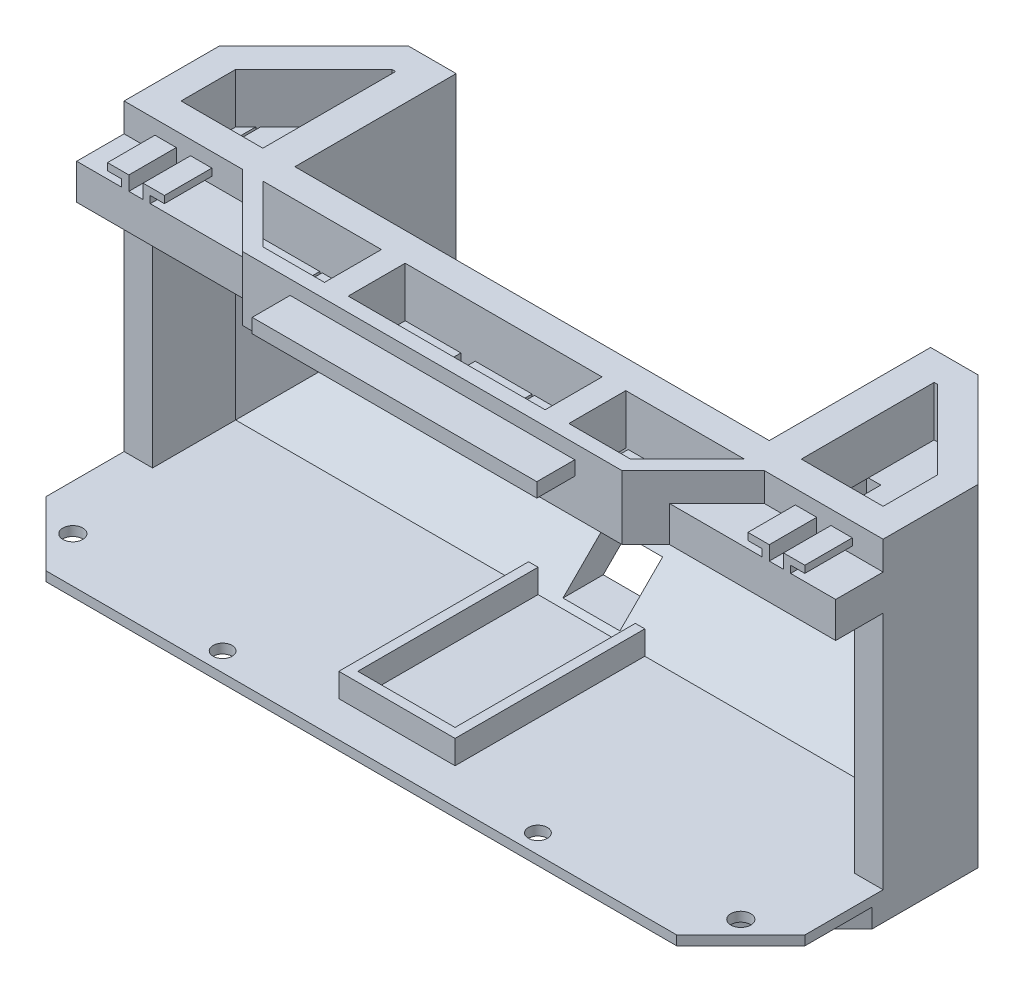
SolidWorks part; units mm, degrees
ref_plane "Front Plane" through (0, 0, 0) normal (0, 0, 1) x (1, 0, 0)
ref_plane "Top Plane" through (0, 0, 0) normal (0, 1, 0) x (1, 0, 0)
ref_plane "Right Plane" through (0, 0, 0) normal (1, 0, 0) x (0, 0, -1)
sketch "Sketch2" plane through (0, 0, 0) normal (0, 1, 0) x (1, 0, 0)
  line L0 (-62.5376, 36.5919) -> (57.4624, 36.5919)
  line L1 (57.4624, 36.5919) -> (77.4624, 16.5919)
  line L2 (77.4624, 16.5919) -> (77.4624, -3.4081)
  line L3 (77.4624, -3.4081) -> (52.4624, -3.4081)
  line L4 (52.4624, -3.4081) -> (37.4624, -18.4081)
  line L5 (37.4624, -18.4081) -> (-42.5376, -18.4081)
  line L6 (-42.5376, -18.4081) -> (-57.5376, -3.4081)
  line L7 (-57.5376, -3.4081) -> (-82.5376, -3.4081)
  line L8 (-82.5376, -3.4081) -> (-82.5376, 16.5919)
  line L9 (-82.5376, 16.5919) -> (-62.5376, 36.5919)
  dimension "D1" = 135
  dimension "D2" = 135
  dimension "D3" = 135
  dimension "D4" = 20
  dimension "D5" = 20
  dimension "D6" = 20
  dimension "D7" = 25
  dimension "D8" = 25
  dimension "D9" = 80
  dimension "D10" = 160
  dimension "D11" = 15
extrude "Boss-Extrude1" add sketch "Sketch2" along normal blind 70
sketch "Sketch3" plane through (0, 0, 0) normal (1, 0, 0) x (0, 0, -1)
  line L0 (16.5919, 0) -> (36.5919, 20)
  line L1 (36.5919, 70) -> (36.5919, 0) construction
  line L2 (36.5919, 20) -> (36.5919, 0)
  line L3 (36.5919, 0) -> (16.5919, 0)
  line L4 (36.5919, 70) -> (16.5919, 70) construction
  dimension "D1" = 50
extrude "Cut-Extrude1" cut sketch "Sketch3" against normal through all both and the other way through all
shell "Shell1" thickness 6
sketch "Sketch5" plane through (0, 0, 0) normal (0, -1, 0) x (1, 0, 0)
  line L0 (-82.5376, -16.5919) -> (-82.5376, 3.4081) construction
  line L1 (77.4624, -16.5919) -> (-82.5376, -16.5919)
  line L2 (77.4624, -16.5919) -> (77.4624, 5.7304)
  line L3 (59.7848, 23.4081) -> (-64.8599, 23.4081)
  line L4 (-82.5376, -16.5919) -> (-82.5376, 5.7304)
  line L5 (-82.5376, 5.7304) -> (-64.8599, 23.4081)
  line L6 (77.4624, 5.7304) -> (59.7848, 23.4081)
  dimension "D1" = 40
  dimension "D2" = 25
  dimension "D3" = 135
  dimension "D4" = 135
  dimension "D5" = 25
extrude "Boss-Extrude2" add sketch "Sketch5" against normal blind 6
sketch "Sketch6" plane through (0, 6, 0) normal (0, 1, 0) x (1, 0, 0)
  line L6 (-82.5376, -5.7304) -> (-82.5376, -19.8726)
  line L7 (77.4624, -5.7304) -> (77.4624, -19.8726)
  line L8 (-82.5376, -5.7304) -> (77.4624, -5.7304)
  line L9 (84.5335, -12.8015) -> (63.9269, -33.4081)
  line L10 (63.9269, -33.4081) -> (-69.002, -33.4081)
  line L11 (-69.002, -33.4081) -> (-89.6086, -12.8015)
  line L12 (77.4624, -19.8726) -> (63.9269, -33.4081)
  line L13 (63.9269, -33.4081) -> (-69.002, -33.4081)
  line L14 (-69.002, -33.4081) -> (-82.5376, -19.8726)
  dimension "D1" = 10
extrude "Boss-Extrude3" add sketch "Sketch6" against normal blind 2
sketch "Sketch7" plane through (0, 4, 0) normal (0, -1, 0) x (1, 0, 0)
  line L0 (70.6947, 26.6403) -> (67.8663, 23.8119) construction
  line L1 (63.9269, 33.4081) -> (77.4624, 19.8726) construction
  line L2 (-2.5376, 33.4081) -> (63.9269, 33.4081) construction
  line L3 (-69.002, 33.4081) -> (63.9269, 33.4081) construction
  line L4 (30.6947, 33.4081) -> (30.6947, 29.4081) construction
  line L5 (-2.5376, 33.4081) -> (-2.5376, 26.6403) construction
  circle A0 centre (67.8663, 23.8119) radius 2.1
  circle A2 centre (30.6947, 29.4081) radius 2
  circle A3 centre (-72.9414, 23.8119) radius 2.1
  circle A4 centre (-35.7698, 29.4081) radius 2
  dimension "D2" = 4.2
  dimension "D4" = 4
  dimension "D1" = 4
  dimension "D3" = 90
  dimension "D5" = 4
extrude "Cut-Extrude5" cut sketch "Sketch7" against normal up to next
sketch "Sketch8" plane through (0, 0, 3.4081) normal (0, 0, 1) x (1, 0, 0)
  line L0 (-70.0376, 70) -> (-70.0376, 64) construction
  line L1 (-82.5376, 70) -> (-57.5376, 70) construction
  line L2 (-60.0523, 64) -> (-76.5376, 64) construction
  line L3 (-42.5376, 70) -> (37.4624, 70) construction
  line L4 (-2.5376, 70) -> (-2.5376, 64) construction
  line L5 (54.9772, 64) -> (-60.0523, 64) construction
  line L6 (-73.0376, 64) -> (-73.0376, 65.5)
  line L7 (-76.5376, 64) -> (-57.5376, 64) construction
  line L8 (-73.0376, 65.5) -> (-76.0376, 65.5)
  line L9 (-76.0376, 65.5) -> (-76.0376, 67)
  line L10 (-76.0376, 67) -> (-71.5376, 67)
  line L11 (-71.5376, 67) -> (-71.5376, 64)
  line L12 (-71.5376, 64) -> (-73.0376, 64)
  line L13 (-68.5376, 67) -> (-68.5376, 64)
  line L14 (-64.0376, 67) -> (-68.5376, 67)
  line L15 (-64.0376, 65.5) -> (-64.0376, 67)
  line L16 (-67.0376, 65.5) -> (-64.0376, 65.5)
  line L17 (-67.0376, 64) -> (-67.0376, 65.5)
  line L18 (-68.5376, 64) -> (-67.0376, 64)
  line L19 (58.9624, 67) -> (63.4624, 67)
  line L20 (58.9624, 65.5) -> (58.9624, 67)
  line L21 (61.9624, 65.5) -> (58.9624, 65.5)
  line L22 (61.9624, 64) -> (61.9624, 65.5)
  line L23 (63.4624, 64) -> (61.9624, 64)
  line L24 (63.4624, 67) -> (63.4624, 64)
  line L25 (66.4624, 67) -> (66.4624, 64)
  line L26 (70.9624, 67) -> (66.4624, 67)
  line L27 (70.9624, 65.5) -> (70.9624, 67)
  line L28 (67.9624, 65.5) -> (70.9624, 65.5)
  line L29 (67.9624, 64) -> (67.9624, 65.5)
  line L30 (66.4624, 64) -> (67.9624, 64)
  point P16 (-76.0376, 66.25)
  point P21 (-72.2876, 64)
  dimension "D1" = 1.5
  dimension "D2" = 1.5
  dimension "D3" = 4.5
  dimension "D4" = 1.5
  dimension "D5" = 3
extrude "Boss-Extrude4" add sketch "Sketch8" along normal blind 10
sketch "Sketch9" plane through (0, 70, 0) normal (0, 1, 0) x (1, 0, 0)
  line L0 (-76.5376, 14.1066) -> (-60.0523, 30.5919)
  line L1 (-60.0523, 30.5919) -> (-59.2949, 30.5919)
  line L2 (-59.2949, 30.5919) -> (-59.2949, 2.5919)
  line L3 (-59.2949, 2.5919) -> (-76.5376, 2.5919)
  line L4 (-76.5376, 2.5919) -> (-76.5376, 14.1066)
  line L5 (-53.2949, -3.4081) -> (-41.2949, -15.4081)
  line L6 (-41.2949, -15.4081) -> (-28.2949, -15.4081)
  line L7 (-28.2949, -15.4081) -> (-28.2949, -3.4081)
  line L8 (-28.2949, -3.4081) -> (-53.2949, -3.4081)
  line L9 (-23.2949, -3.4081) -> (-23.2949, -15.4081)
  line L13 (-2.5376, -18.4081) -> (-2.5376, 12.4152) construction
  line L14 (-42.5376, -18.4081) -> (37.4624, -18.4081) construction
  line L15 (-23.2949, -3.4081) -> (18.2198, -3.4081)
  line L16 (-23.2949, -15.4081) -> (18.2198, -15.4081)
  line L17 (-53.2949, -3.4081) -> (-60.2217, 3.5186) construction
  line L18 (-57.5376, -3.4081) -> (-42.5376, -18.4081) construction
  line L19 (-82.5376, -3.4081) -> (-57.5376, -3.4081) construction
  line L20 (-62.5376, 36.5919) -> (-82.5376, 16.5919) construction
  line L21 (-82.5376, 16.5919) -> (-82.5376, -3.4081) construction
  line L22 (57.4624, 36.5919) -> (-62.5376, 36.5919) construction
  line L23 (18.2198, -3.4081) -> (18.2198, -15.4081)
  line L24 (23.2198, -15.4081) -> (23.2198, -3.4081)
  line L25 (36.2198, -15.4081) -> (23.2198, -15.4081)
  line L26 (48.2198, -3.4081) -> (36.2198, -15.4081)
  line L27 (23.2198, -3.4081) -> (48.2198, -3.4081)
  line L28 (54.2198, 2.5919) -> (71.4624, 2.5919)
  line L29 (54.2198, 30.5919) -> (54.2198, 2.5919)
  line L30 (54.9772, 30.5919) -> (54.2198, 30.5919)
  line L31 (71.4624, 14.1066) -> (54.9772, 30.5919)
  line L32 (71.4624, 2.5919) -> (71.4624, 14.1066)
  point P25 (-76.5376, 8.3492)
  point P31 (-2.5376, -15.4081)
  point P32 (-2.5376, -3.4081)
  dimension "D1" = 135
  dimension "D2" = 3
  dimension "D3" = 3
  dimension "D4" = 6
  dimension "D5" = 6
  dimension "D6" = 6
  dimension "D7" = 6
  dimension "D8" = 12
  dimension "D9" = 5
  dimension "D10" = 25
extrude "Cut-Extrude6" cut sketch "Sketch9" against normal up to next
sketch "Sketch10" plane through (0, 0, 0) normal (0, 0, 1) x (1, 0, 0)
  line L1 (-82.5376, 0) -> (77.4624, 0) construction
  line L2 (-8.5376, 7) -> (-8.5376, 16)
  line L3 (-8.5376, 16) -> (3.4624, 16)
  line L4 (3.4624, 16) -> (3.4624, 7)
  line L7 (-2.5376, 0) -> (-2.5376, 7) construction
  line L8 (-2.5376, 7) -> (-8.5376, 7)
  line L9 (-2.5376, 7) -> (3.4624, 7)
  dimension "D1" = 12
  dimension "D2" = 7
  dimension "D3" = 9
extrude "Cut-Extrude7" cut sketch "Sketch10" against normal through all
sketch "Sketch11" plane through (0, 0, 18.4081) normal (0, 0, 1) x (1, 0, 0)
  line L0 (54.2198, 64) -> (-59.2949, 64) construction
  line L1 (-32.5376, 64) -> (27.4624, 64)
  line L2 (-32.5376, 64) -> (-32.5376, 67)
  line L3 (-32.5376, 67) -> (27.4624, 67)
  line L4 (27.4624, 64) -> (27.4624, 67)
  line L5 (-42.5376, 70) -> (37.4624, 70) construction
  point P6 (-2.5376, 67)
  point P9 (-2.5376, 70)
  dimension "D1" = 3
  dimension "D2" = 60
extrude "Boss-Extrude5" add sketch "Sketch11" along normal blind 8
sketch "Sketch12" plane through (0, 70, 0) normal (0, 1, 0) x (1, 0, 0)
  line L0 (57.4624, 36.5919) -> (-62.5376, 36.5919) construction
  line L1 (-52.5376, 2.5919) -> (47.4624, 2.5919)
  line L2 (-52.5376, 2.5919) -> (-52.5376, 36.5919)
  line L3 (-52.5376, 36.5919) -> (47.4624, 36.5919)
  line L4 (47.4624, 2.5919) -> (47.4624, 36.5919)
  line L7 (18.2198, -3.4081) -> (-23.2949, -3.4081) construction
  line L8 (27.4624, -26.4081) -> (-32.5376, -26.4081) construction
  point P6 (-2.5376, 36.5919)
  point P9 (-2.5376, -26.4081)
  dimension "D1" = 100
  dimension "D3" = 6
extrude "Cut-Extrude8" cut sketch "Sketch12" against normal blind 50
sketch "Sketch13" plane through (0, 20, 0) normal (0, 1, 0) x (1, 0, 0)
  line L0 (47.4624, 28.1066) -> (47.4624, 36.5919) construction
  line L1 (-52.5376, 28.1066) -> (43.9772, 28.1066)
  line L3 (-49.0523, 30.5919) -> (47.4624, 30.5919)
  line L5 (47.4624, 30.5919) -> (54.9772, 30.5919) construction
  line L6 (-59.2949, 2.5919) -> (-59.2949, 30.5919) construction
  line L7 (-49.0523, 30.5919) -> (-56.2949, 30.5919)
  line L9 (-52.5376, 28.1066) -> (-56.2949, 28.1066)
  line L10 (-56.2949, 30.5919) -> (-56.2949, 28.1066)
  line L11 (47.4624, 30.5919) -> (51.2198, 30.5919)
  line L13 (43.9772, 28.1066) -> (51.2198, 28.1066)
  line L14 (51.2198, 30.5919) -> (51.2198, 28.1066)
  line L15 (54.2198, 30.5919) -> (54.2198, 2.5919) construction
  dimension "D1" = 3
  dimension "D2" = 3
extrude "Boss-Extrude8" add sketch "Sketch13" along normal blind 7
sketch "Sketch14" plane through (0, 20, 0) normal (0, 1, 0) x (1, 0, 0)
  line L0 (47.4624, 30.5919) -> (47.4624, 36.5919) construction
  line L1 (-52.5376, 36.5919) -> (47.4624, 36.5919)
  line L2 (-52.5376, 36.5919) -> (-52.5376, 33.5919)
  line L3 (-52.5376, 33.5919) -> (47.4624, 33.5919)
  line L4 (47.4624, 36.5919) -> (47.4624, 33.5919)
extrude "Boss-Extrude9" add sketch "Sketch14" along normal blind 10
sketch "Sketch15" plane through (0, 0, -2.5919) normal (0, 0, -1) x (-1, 0, 0)
  line L0 (52.5376, 30) -> (52.5376, 70) construction
  line L1 (-47.4624, 64) -> (52.5376, 64)
  line L2 (-47.4624, 64) -> (-47.4624, 66)
  line L3 (-47.4624, 66) -> (52.5376, 66)
  line L4 (52.5376, 64) -> (52.5376, 66)
  dimension "D1" = 2
extrude "Boss-Extrude10" add sketch "Sketch15" along normal blind 3
sketch "Sketch16" plane through (0, 6, 0) normal (0, 1, 0) x (1, 0, 0)
  line L0 (-76.5376, 14.1066) -> (71.4624, 14.1066) construction
  line L1 (-12.7876, -23.8934) -> (7.7124, -23.8934)
  line L2 (-12.7876, -23.8934) -> (-12.7876, -25.8934)
  line L3 (-12.7876, -25.8934) -> (7.7124, -25.8934)
  line L4 (7.7124, -23.8934) -> (7.7124, -25.8934)
  line L6 (7.7124, -25.8934) -> (9.7124, -25.8934)
  line L7 (7.7124, -25.8934) -> (7.7124, 14.1066)
  line L8 (7.7124, 14.1066) -> (9.7124, 14.1066)
  line L9 (9.7124, -25.8934) -> (9.7124, 14.1066)
  line L10 (-12.7876, -25.8934) -> (-14.7876, -25.8934)
  line L11 (-12.7876, -25.8934) -> (-12.7876, 14.1066)
  line L12 (-12.7876, 14.1066) -> (-14.7876, 14.1066)
  line L13 (-14.7876, -25.8934) -> (-14.7876, 14.1066)
  point P12 (-2.5376, -23.8934)
  point P13 (-2.5376, 14.1066)
  line M22 (71.4624, 14.1066) -> (-76.5376, 14.1066)
  dimension "D1" = 38
  dimension "D2" = 2
  dimension "D3" = 20.5
  dimension "D4" = 2
  dimension "D5" = 2
extrude "Boss-Extrude11" add sketch "Sketch16" along normal blind 5 contours L13 L10 L2 L11 M22 | L4 L1 L2 L3 | L6 L9 L7 L4 M22
ref_plane "Plane1" through (0, 59.5, 0) normal (0, 1, 0) x (1, 0, 0)
sketch "Sketch17" plane through (0, 59.5, 0) normal (0, 1, 0) x (1, 0, 0)
  line L0 (-76.5376, 14.1066) -> (-60.0523, 30.5919)
  line L1 (-60.0523, 30.5919) -> (-56.2949, 30.5919)
  line L2 (-60.0523, 30.5919) -> (-56.2949, 30.5919) construction
  line L3 (-56.2949, 30.5919) -> (-56.2949, -0.4081)
  line L6 (-59.2949, 2.5919) -> (-59.2949, 30.5919) construction
  line L8 (-76.5376, 14.1066) -> (-76.5376, -0.4081)
  line L22 (51.2198, 30.5919) -> (54.9772, 30.5919)
  line L23 (-25.2949, -18.4081) -> (-25.2949, -0.4081)
  line L24 (-42.5376, -18.4081) -> (-25.2949, -18.4081)
  line L25 (-60.5376, -0.4081) -> (-42.5376, -18.4081)
  line L26 (-25.2949, -0.4081) -> (-60.5376, -0.4081)
  line L28 (-42.5376, -18.4081) -> (-25.2949, -18.4081)
  line L29 (-60.5376, -0.4081) -> (-42.5376, -18.4081)
  line L30 (-25.2949, -0.4081) -> (-56.2949, -0.4081)
  line L31 (21.2198, -0.4081) -> (21.2198, -18.4081)
  line L32 (21.2198, -18.4081) -> (37.4624, -18.4081)
  line L33 (37.4624, -18.4081) -> (55.4624, -0.4081)
  line L34 (55.4624, -0.4081) -> (21.2198, -0.4081)
  line L36 (21.2198, -18.4081) -> (37.4624, -18.4081)
  line L38 (37.4624, -18.4081) -> (55.4624, -0.4081)
  line L39 (51.2198, -0.4081) -> (21.2198, -0.4081)
  line L40 (54.9772, 30.5919) -> (71.4624, 14.1066)
  line L41 (21.2198, -18.4081) -> (21.2198, -0.4081)
  line L42 (21.2198, -0.4081) -> (-25.2949, -0.4081)
  line L43 (-25.2949, -0.4081) -> (-25.2949, -18.4081)
  line L44 (-25.2949, -18.4081) -> (21.2198, -18.4081)
  line L45 (-76.5376, 2.5919) -> (-59.2949, 2.5919) construction
  line L46 (21.2198, -0.4081) -> (-25.2949, -0.4081)
  line L48 (-25.2949, -18.4081) -> (21.2198, -18.4081)
  line L49 (51.2198, -0.4081) -> (71.4624, -0.4081)
  line L50 (51.2198, 30.5919) -> (51.2198, -0.4081)
  line L51 (55.4624, -0.4081) -> (71.4624, -0.4081)
  line L52 (51.2198, 30.5919) -> (51.2198, -0.4081)
  line L53 (71.4624, 14.1066) -> (71.4624, -0.4081)
  line L54 (-76.5376, -0.4081) -> (-60.5376, -0.4081)
  dimension "D1" = 3
  dimension "D2" = 3
  dimension "D3" = 3
  dimension "D4" = 3
  dimension "D5" = 3
  dimension "D6" = 3
extrude "Boss-Extrude12" add sketch "Sketch17" against normal blind 3
sketch "Sketch18" plane through (0, 59.5, 0) normal (0, 1, 0) x (1, 0, 0)
  line L0 (-56.2949, 30.5919) -> (-59.2949, 30.5919)
  line L1 (-59.2949, 30.5919) -> (-59.2949, 2.5919)
  line L2 (-59.2949, 2.5919) -> (-76.5376, 2.5919)
  line L3 (-76.5376, 2.5919) -> (-76.5376, -0.4081)
  line L4 (-76.5376, -0.4081) -> (-60.5376, -0.4081)
  line L5 (-60.5376, -0.4081) -> (-42.5376, -18.4081)
  line L6 (-42.5376, -18.4081) -> (37.4624, -18.4081)
  line L7 (37.4624, -18.4081) -> (55.4624, -0.4081)
  line L8 (55.4624, -0.4081) -> (71.4624, -0.4081)
  line L9 (71.4624, -0.4081) -> (71.4624, 2.5919)
  line L10 (71.4624, 2.5919) -> (54.2198, 2.5919)
  line L11 (54.2198, 2.5919) -> (54.2198, 30.5919)
  line L12 (54.2198, 30.5919) -> (51.2198, 30.5919)
  line L13 (51.2198, 30.5919) -> (51.2198, -0.4081)
  line L14 (51.2198, -0.4081) -> (-56.2949, -0.4081)
  line L15 (-56.2949, -0.4081) -> (-56.2949, 30.5919)
  line L16 (-53.2949, -3.4081) -> (-41.2949, -15.4081)
  line L17 (-41.2949, -15.4081) -> (-28.2949, -15.4081)
  line L18 (-28.2949, -15.4081) -> (-28.2949, -3.4081)
  line L19 (-28.2949, -3.4081) -> (-53.2949, -3.4081)
  line L20 (18.2198, -3.4081) -> (-23.2949, -3.4081)
  line L21 (-23.2949, -3.4081) -> (-23.2949, -15.4081)
  line L22 (-23.2949, -15.4081) -> (18.2198, -15.4081)
  line L23 (18.2198, -15.4081) -> (18.2198, -3.4081)
  line L24 (23.2198, -3.4081) -> (23.2198, -15.4081)
  line L25 (23.2198, -15.4081) -> (36.2198, -15.4081)
  line L26 (36.2198, -15.4081) -> (48.2198, -3.4081)
  line L27 (48.2198, -3.4081) -> (23.2198, -3.4081)
extrude "Boss-Extrude13" add sketch "Sketch18" along normal up to surface (10.5 mm away) up to face at (-66.3434, 70, -16.0948)
sketch "Sketch19" plane through (0, 59.5, 0) normal (0, 1, 0) x (1, 0, 0)
  line L0 (-41.2949, -15.4081) -> (-28.2949, -15.4081) construction
  line L1 (-28.7949, -3.4081) -> (-40.7949, -3.4081) construction
  line L2 (-28.7949, -3.4081) -> (-28.7949, -15.4081) construction
  line L3 (-28.7949, -15.4081) -> (-40.7949, -15.4081) construction
  line L4 (-40.7949, -3.4081) -> (-40.7949, -15.4081) construction
  line L5 (-61.9162, 16.7279) -> (-73.9162, 16.7279) construction
  line L6 (-61.9162, 16.7279) -> (-61.9162, 4.7279) construction
  line L7 (-61.9162, 4.7279) -> (-73.9162, 4.7279) construction
  line L8 (-73.9162, 16.7279) -> (-73.9162, 4.7279) construction
  line L9 (3.4624, -3.4081) -> (-8.5376, -3.4081) construction
  line L10 (3.4624, -3.4081) -> (3.4624, -15.4081) construction
  line L11 (3.4624, -15.4081) -> (-8.5376, -15.4081) construction
  line L12 (-8.5376, -3.4081) -> (-8.5376, -15.4081) construction
  line L13 (35.7198, -3.4081) -> (23.7198, -3.4081) construction
  line L14 (35.7198, -3.4081) -> (35.7198, -15.4081) construction
  line L15 (35.7198, -15.4081) -> (23.7198, -15.4081) construction
  line L16 (23.7198, -3.4081) -> (23.7198, -15.4081) construction
  line L17 (68.8411, 16.7279) -> (56.8411, 16.7279) construction
  line L18 (68.8411, 16.7279) -> (68.8411, 4.7279) construction
  line L19 (68.8411, 4.7279) -> (56.8411, 4.7279) construction
  line L20 (56.8411, 16.7279) -> (56.8411, 4.7279) construction
  line L21 (-28.2949, -15.4081) -> (-28.2949, -3.4081) construction
  line L23 (36.2198, -15.4081) -> (35.7198, -15.4081)
  line L24 (-60.0523, 30.5919) -> (-76.5376, 14.1066) construction
  line L25 (71.4624, 14.1066) -> (54.9772, 30.5919) construction
  line L26 (35.7198, -15.4081) -> (35.7198, -3.4081)
  line L27 (35.7198, -3.4081) -> (36.2198, -3.4081)
  line L28 (35.7198, -3.9081) -> (36.2198, -3.9081)
  line L29 (-23.2949, -15.4081) -> (18.2198, -15.4081) construction
  line L30 (18.2198, -15.4081) -> (18.2198, -3.4081) construction
  line L31 (23.2198, -15.4081) -> (36.2198, -15.4081) construction
  line L32 (-76.5376, 2.5919) -> (-59.2949, 2.5919) construction
  line L33 (54.2198, 2.5919) -> (71.4624, 2.5919) construction
  line L34 (-61.4162, 16.7279) -> (-61.4162, 4.7279)
  line L35 (-74.4162, 16.2279) -> (-74.4162, 4.7279)
  line L36 (-73.9162, 16.7279) -> (-74.4162, 16.2279)
  line L37 (-60.0523, 30.5919) -> (-76.5376, 14.1066) construction
  line L38 (-74.4162, 4.7279) -> (-73.9162, 4.7279)
  line L39 (-74.4162, 16.7279) -> (-74.4162, 4.7279) construction
  line L40 (-73.9162, 4.7279) -> (-73.9162, 16.7279)
  line L41 (-61.4162, 16.7279) -> (-61.9162, 16.7279)
  line L42 (-61.9162, 16.7279) -> (-61.9162, 4.7279)
  line L43 (-61.9162, 4.7279) -> (-61.4162, 4.7279)
  line L44 (-41.2949, -3.4081) -> (-41.2949, -15.4081)
  line L45 (-28.7949, -3.4081) -> (-28.2949, -3.4081)
  line L46 (-28.2949, -3.4081) -> (-28.2949, -15.4081)
  line L47 (-28.2949, -15.4081) -> (-28.7949, -15.4081)
  line L48 (-28.7949, -15.4081) -> (-28.7949, -3.4081)
  line L49 (-41.2949, -15.4081) -> (-40.7949, -15.4081)
  line L50 (-40.7949, -15.4081) -> (-40.7949, -3.4081)
  line L51 (-40.7949, -3.4081) -> (-41.2949, -3.4081)
  line L52 (-9.0376, -3.4081) -> (-9.0376, -15.4081)
  line L53 (3.9624, -3.4081) -> (3.9624, -15.4081)
  line L54 (-9.0376, -3.4081) -> (-8.5376, -3.4081)
  line L55 (-8.5376, -3.4081) -> (-8.5376, -15.4081)
  line L56 (-8.5376, -15.4081) -> (-9.0376, -15.4081)
  line L57 (3.9624, -3.4081) -> (3.4624, -3.4081)
  line L58 (3.4624, -3.4081) -> (3.4624, -15.4081)
  line L59 (3.4624, -15.4081) -> (3.9624, -15.4081)
  line L60 (36.2198, -3.4081) -> (36.2198, -15.4081)
  line L61 (23.7198, -3.4081) -> (23.2198, -3.4081)
  line L62 (23.2198, -3.4081) -> (23.2198, -15.4081)
  line L63 (23.2198, -15.4081) -> (23.7198, -15.4081)
  line L64 (23.7198, -15.4081) -> (23.7198, -3.4081)
  line L66 (56.3411, 16.7279) -> (56.3411, 4.7279)
  line L71 (56.3411, 4.7279) -> (56.8411, 4.7279)
  line L72 (56.8411, 4.7279) -> (56.8411, 16.7279)
  line L73 (56.8411, 16.7279) -> (56.3411, 16.7279)
  line L75 (69.3411, 16.2279) -> (69.3411, 4.7279)
  line L76 (68.8411, 16.7279) -> (69.3411, 16.2279)
  line L77 (71.4624, 14.1066) -> (54.9772, 30.5919) construction
  line L78 (69.3411, 4.7279) -> (68.8411, 4.7279)
  line L79 (68.8411, 4.7279) -> (68.8411, 16.7279)
  line L81 (69.3411, 16.7279) -> (69.3411, 4.7279) construction
  point P20 (-34.7949, -15.4081)
  point P23 (-34.7949, -15.4081)
  point P26 (-28.2949, -9.4081)
  point P27 (-28.7949, -9.4081)
  point P28 (-67.9162, 4.7279)
  point P31 (-67.9162, 2.5919)
  point P32 (62.8411, 4.7279)
  point P35 (62.8411, 2.5919)
  point P47 (-2.5376, -15.4081)
  point P50 (-2.5376, -15.4081)
  point P51 (3.4624, -9.4081)
  point P54 (18.2198, -9.4081)
  point P55 (29.7198, -15.4081)
  point P58 (29.7198, -15.4081)
  point P77 (69.3411, 16.7279)
  point P78 (69.3411, 4.7279)
  dimension "D1" = 12
  dimension "D2" = 12
  dimension "D3" = 0.5
  dimension "D4" = 0.5
  dimension "D5" = 0.5
  dimension "D6" = 0.5
  dimension "D7" = 0.5
  dimension "D8" = 0.5
  dimension "D9" = 0.5
  dimension "D10" = 0.5
extrude "Cut-Extrude10" cut sketch "Sketch19" against normal up to surface (3 mm away) contours L34 L43 L42 L41 | L35 L38 L40 L36 | L50 L51 L44 L49 | L46 L47 L48 L45 | L55 L56 L52 L54 | L53 L59 L58 L57 | L64 L61 L62 L63 | L60 L23 L26 L27 | L66 L71 L72 L73 | L79 L76 L75 L78 up to face at (-2.5376, 56.5, -7.9511)
sketch "Sketch21" plane through (0, 56.5, 0) normal (0, -1, 0) x (-1, 0, 0)
  line L0 (61.4162, 4.7279) -> (61.9162, 4.7279) construction
  line L1 (28.7949, -15.4081) -> (25.7949, -15.4081)
  line L2 (28.7949, -15.4081) -> (28.7949, -3.4081)
  line L3 (28.7949, -3.4081) -> (25.7949, -3.4081)
  line L4 (25.7949, -15.4081) -> (25.7949, -3.4081)
  line L5 (61.9162, 16.7279) -> (58.9162, 16.7279)
  line L6 (61.9162, 16.7279) -> (61.9162, 4.7279)
  line L7 (61.9162, 4.7279) -> (58.9162, 4.7279)
  line L8 (58.9162, 16.7279) -> (58.9162, 4.7279)
  line L9 (8.5376, -3.4081) -> (9.0376, -3.4081) construction
  line L10 (8.5376, -15.4081) -> (11.5376, -15.4081)
  line L11 (8.5376, -15.4081) -> (8.5376, -3.4081)
  line L12 (8.5376, -3.4081) -> (11.5376, -3.4081)
  line L13 (11.5376, -15.4081) -> (11.5376, -3.4081)
  line L14 (-56.3411, 16.7279) -> (-56.8411, 16.7279) construction
  line L15 (-23.7198, -15.4081) -> (-20.7198, -15.4081)
  line L16 (-23.7198, -15.4081) -> (-23.7198, -3.4081)
  line L17 (-23.7198, -3.4081) -> (-20.7198, -3.4081)
  line L18 (-20.7198, -15.4081) -> (-20.7198, -3.4081)
  line L19 (-56.8411, 4.7279) -> (-53.8411, 4.7279)
  line L20 (-56.8411, 4.7279) -> (-56.8411, 16.7279)
  line L21 (-56.8411, 16.7279) -> (-53.8411, 16.7279)
  line L22 (-53.8411, 4.7279) -> (-53.8411, 16.7279)
  line L23 (-23.2198, -3.4081) -> (-23.7198, -3.4081) construction
  dimension "D1" = 3
  dimension "D2" = 3
  dimension "D3" = 3
  dimension "D4" = 3
  dimension "D5" = 3
extrude "Cut-Extrude11" cut sketch "Sketch21" against normal up to surface (3 mm away) up to face at (-69.8202, 59.5, -13.654)
sketch "Sketch22" plane through (0, 0, 0) normal (1, 0, 0) x (0, 0, -1)
  line L0 (5.5919, 66) -> (30.5919, 30)
  line L1 (30.5919, 56.5) -> (30.5919, 22.4853) construction
  line L2 (30.5919, 30) -> (30.5919, 27)
  line L3 (30.5919, 27) -> (28.1066, 27)
  line L4 (3.1278, 64.2888) -> (28.1278, 28.2888)
  line L5 (28.1066, 27) -> (28.1278, 28.2888)
  line L6 (3.1278, 64.2888) -> (5.5919, 66)
  dimension "D1" = 3
sketch "Sketch23" plane through (0, 27, 0) normal (0, 1, 0) x (1, 0, 0)
  line L0 (-52.5376, 36.5919) -> (-52.5376, 2.5919) construction
  line L1 (-56.2949, 30.5919) -> (-52.5376, 30.5919)
  line L2 (-56.2949, 30.5919) -> (-56.2949, 2.5919)
  line L3 (-56.2949, 2.5919) -> (-52.5376, 2.5919)
  line L4 (-52.5376, 30.5919) -> (-52.5376, 2.5919)
  line L5 (51.2198, 30.5919) -> (47.4624, 30.5919)
  line L6 (51.2198, 30.5919) -> (51.2198, 2.5919)
  line L7 (51.2198, 2.5919) -> (47.4624, 2.5919)
  line L8 (47.4624, 30.5919) -> (47.4624, 2.5919)
  line L9 (-52.5376, 2.5919) -> (47.4624, 2.5919) construction
  line L10 (47.4624, 2.5919) -> (47.4624, 36.5919) construction
extrude "Boss-Extrude15" add sketch "Sketch23" along normal up to surface (37 mm away)
extrude "Boss-Extrude16" add sketch "Sketch22" along normal up to surface (100 mm away) from surface at -52.5376 up to face at (47.4624, 44.6923, -19.3238) starting at face at (-52.5376, 44.6923, -19.3238)
sketch "Sketch24" plane through (0, 3.8155, -48.7755) normal (0, 0.5704, -0.8214) x (-1, 0, 0)
  line L0 (52.5376, 77.4194) -> (-47.4624, 77.4194) construction
  line L2 (52.5376, 75.7082) -> (-47.4624, 75.7082) construction
  circle A0 centre (2.5376, 57.7082) radius 5
  point P5 (2.5376, 77.4194)
  dimension "D2" = 10
  dimension "D1" = 18
extrude "Cut-Extrude12" cut sketch "Sketch24" against normal up to surface (3 mm away) up to face at (-2.5376, 46.1444, -15.7281)
sketch "Sketch26" plane through (0, 0, 0) normal (1, 0, 0) x (0, 0, -1)
  line L0 (28.1066, 27) -> (28.1278, 28.2888)
  line L1 (28.1278, 28.2888) -> (3.3283, 64)
  line L2 (3.3283, 64) -> (2.5919, 64)
  line L3 (2.5919, 64) -> (2.5919, 27)
  line L4 (2.5919, 27) -> (28.1066, 27)
extrude "Cut-Extrude13" cut sketch "Sketch26" along normal up to surface (107.5147 mm away) from surface at -56.2949 up to face at (51.2198, 34.9142, -20.4301) starting at face at (-56.2949, 34.9142, -20.4301)
sketch "Sketch27" plane through (0, 64, 0) normal (0, -1, 0) x (1, 0, 0)
  line L0 (-60.5376, 0.4081) -> (-42.5376, 18.4081) construction
  line L1 (-82.5376, 0.4081) -> (-56.2949, 0.4081)
  line L2 (-82.5376, 0.4081) -> (-82.5376, 13.4081)
  line L3 (-82.5376, 13.4081) -> (-47.5376, 13.4081)
  line L4 (-47.5376, 9.1655) -> (-47.5376, 13.4081)
  line L5 (-76.0376, 13.4081) -> (-73.0376, 13.4081) construction
  line L6 (-76.5376, 0.4081) -> (-60.5376, 0.4081) construction
  line L7 (-82.5376, 5.7304) -> (-82.5376, 19.8726) construction
  line L8 (-2.5376, 33.4081) -> (-2.5376, 46.5844) construction
  line L9 (-69.002, 33.4081) -> (63.9269, 33.4081) construction
  line L14 (-56.2949, 0.4081) -> (-47.5376, 9.1655)
  line L15 (-53.2949, 3.4081) -> (-41.2949, 15.4081) construction
  line L16 (77.4624, 0.4081) -> (77.4624, 13.4081)
  line L17 (77.4624, 0.4081) -> (51.2198, 0.4081)
  line L18 (51.2198, 0.4081) -> (42.4624, 9.1655)
  line L19 (42.4624, 9.1655) -> (42.4624, 13.4081)
  line L20 (77.4624, 13.4081) -> (42.4624, 13.4081)
extrude "Boss-Extrude17" add sketch "Sketch27" along normal up to surface (7.5 mm away) up to face at (35.9698, 56.5, 9.4081)
sketch "Sketch28" plane through (0, 0, -28.1066) normal (0, 0, 1) x (1, 0, 0)
  line L0 (-2.5376, 20) -> (-2.5376, 28.2888) construction
  line L1 (-56.2949, 20) -> (51.2198, 20) construction
  line L2 (51.2198, 28.2888) -> (-56.2949, 28.2888) construction
  circle A0 centre (17.4624, 24.1444) radius 1.95
  circle A1 centre (-22.5376, 24.1444) radius 1.95
  point P8 (0, 0)
  point P9 (-2.5376, 24.1444)
  point P13 (-2.5376, 20)
  dimension "D1" = 3.9
  dimension "D2" = 20
extrude "Cut-Extrude14" cut sketch "Sketch28" against normal up to surface (5.4853 mm away)
